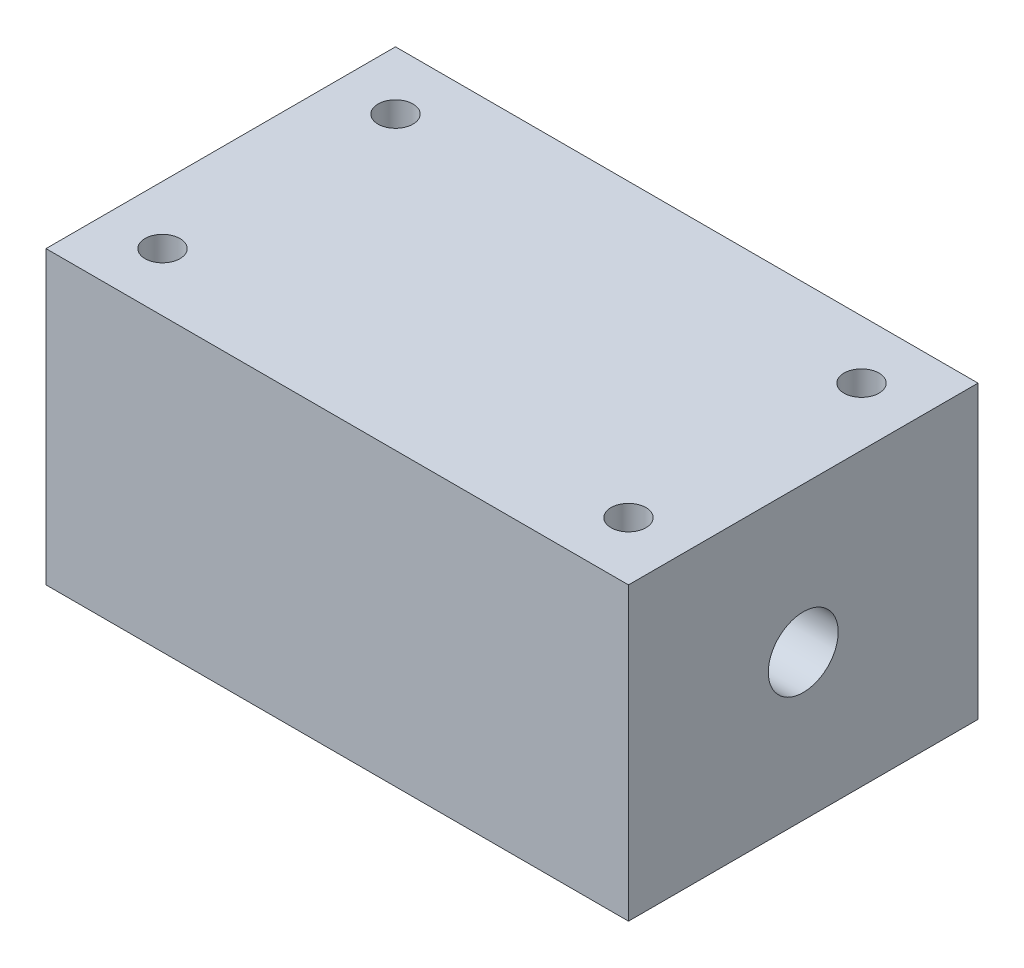
SolidWorks part; units mm, degrees
ref_plane "Plan de face" through (0, 0, 0) normal (0, 0, 1) x (1, 0, 0)
ref_plane "Plan de dessus" through (0, 0, 0) normal (0, 1, 0) x (1, 0, 0)
ref_plane "Plan de droite" through (0, 0, 0) normal (1, 0, 0) x (0, 0, -1)
sketch "Esquisse1" plane through (0, 0, 0) normal (0, 1, 0) x (1, 0, 0)
  line L0 (0, 15) -> (0, -15) construction
  line L1 (-25, -15) -> (25, -15)
  line L2 (-25, -15) -> (-25, 15)
  line L3 (-25, 15) -> (25, 15)
  line L4 (25, -15) -> (25, 15)
  line L5 (-25, -15) -> (25, 15) construction
  line L6 (-25, 15) -> (25, -15) construction
  line L8 (25, 0) -> (-25, 0) construction
  circle A0 centre (-20, 10) radius 1.5
  circle A1 centre (-20, -10) radius 1.5
  circle A2 centre (20, -10) radius 1.5
  circle A3 centre (20, 10) radius 1.5
  point P0 (0, 0)
  dimension "D3" = 3
  dimension "D4" = 10
  dimension "D1" = 30
  dimension "D2" = 50
  dimension "D5" = 20
extrude "Boss.-Extru.1" add sketch "Esquisse1" along normal blind 25
sketch "Esquisse2" plane through (-25, 0, 0) normal (-1, 0, 0) x (0, 0, 1)
  line L0 (0, 0) -> (0, 25) construction
  line L1 (-15, 25) -> (15, 25) construction
  line L3 (-15, 25) -> (-15, 0) construction
  line L4 (-15, 12.5) -> (15, 12.5) construction
  line L5 (15, 25) -> (15, 0) construction
  circle A0 centre (0, 12.5) radius 3
  dimension "D1" = 6
extrude "Enlèv. mat.-Extru.1" cut sketch "Esquisse2" against normal up to next
